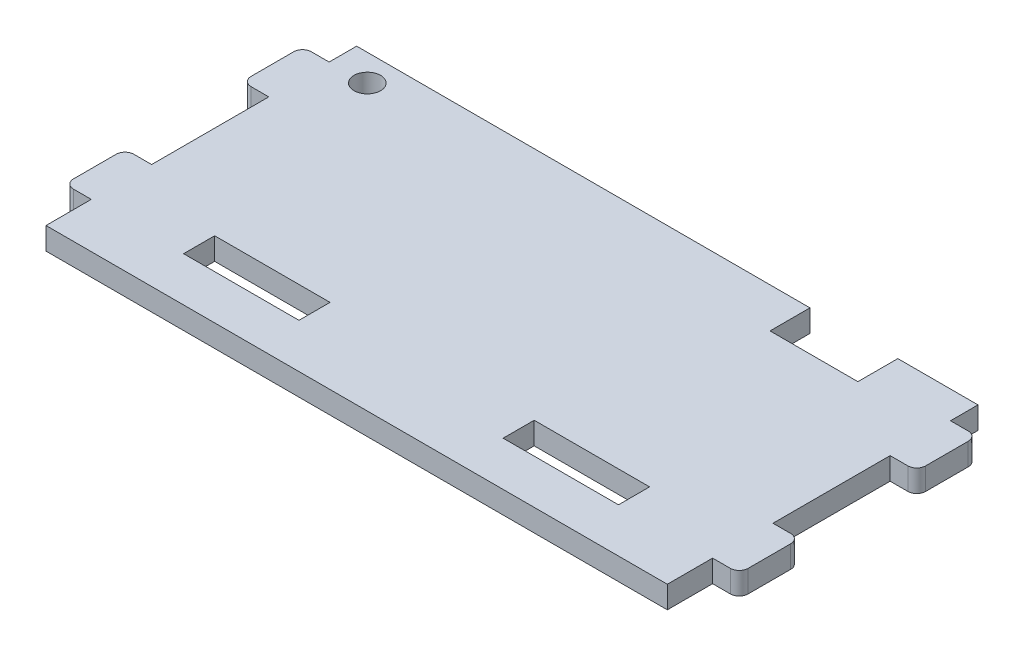
SolidWorks part; units mm, degrees
ref_plane "前视" through (0, 0, 0) normal (0, 0, 1) x (1, 0, 0)
ref_plane "上视" through (0, 0, 0) normal (0, 1, 0) x (1, 0, 0)
ref_plane "右视" through (0, 0, 0) normal (1, 0, 0) x (0, 0, -1)
sketch "草图1" plane through (0, 0, 0) normal (0, 1, 0) x (1, 0, 0)
  line L1 (-38, 17.5) -> (38, 17.5)
  line L2 (-38, 17.5) -> (-38, -17.5)
  line L3 (-38, -17.5) -> (38, -17.5)
  line L4 (38, 17.5) -> (38, -17.5)
  line L5 (-38, 17.5) -> (38, -17.5) construction
  line L6 (-38, -17.5) -> (38, 17.5) construction
  point P0 (0, 0)
  dimension "D1" = 35
  dimension "D2" = 76
extrude "凸台-拉伸1" add sketch "草图1" along normal blind 2.5
sketch "草图2" plane through (0, 2.5, 0) normal (0, 1, 0) x (1, 0, 0)
  line L0 (-38, -17.5) -> (38, -17.5) construction
  line L1 (-24.5, -9) -> (-11.5, -9)
  line L2 (-24.5, -9) -> (-24.5, -12.5)
  line L3 (-24.5, -12.5) -> (-11.5, -12.5)
  line L4 (-11.5, -9) -> (-11.5, -12.5)
  line L5 (-24.5, -9) -> (-11.5, -12.5) construction
  line L6 (-24.5, -12.5) -> (-11.5, -9) construction
  line L7 (-38, 17.5) -> (-38, -17.5) construction
  line L8 (0, 0) -> (0, -2.6782) construction
  line L9 (24.5, -12.5) -> (11.5, -12.5)
  line L10 (11.5, -9) -> (11.5, -12.5)
  line L11 (24.5, -9) -> (11.5, -9)
  line L12 (24.5, -9) -> (24.5, -12.5)
  point P0 (-18, -10.75)
  dimension "D1" = 5
  dimension "D2" = 13.5
  dimension "D3" = 13
  dimension "D4" = 3.5
extrude "切除-拉伸1" cut sketch "草图2" against normal through all
sketch "草图3" plane through (0, 2.5, 0) normal (0, 1, 0) x (1, 0, 0)
  line L0 (-38, -17.5) -> (-35, -17.5)
  line L1 (-38, -17.5) -> (38, -17.5) construction
  line L2 (-35, -17.5) -> (-35, -12.4)
  line L3 (-35, -12.4) -> (-38, -12.4)
  line L4 (-38, 17.5) -> (-38, -17.5) construction
  line L5 (-38, -12.4) -> (-38, -17.5)
  line L6 (-38, 17.5) -> (-35, 17.5)
  line L7 (38, 17.5) -> (-38, 17.5) construction
  line L8 (-35, 17.5) -> (-35, 14.4)
  line L9 (-35, 14.4) -> (-38, 14.4)
  line L10 (-38, 14.4) -> (-38, 17.5)
  line L11 (-38, 7.6) -> (-35, 7.6)
  line L12 (-35, 7.6) -> (-35, -5.6)
  line L13 (-35, -5.6) -> (-38, -5.6)
  line L14 (-38, -5.6) -> (-38, 7.6)
  line L15 (0, 0) -> (0, 5.419) construction
  line L16 (38, -17.5) -> (35, -17.5)
  line L17 (38, -12.4) -> (38, -17.5)
  line L18 (35, -17.5) -> (35, -12.4)
  line L19 (35, -12.4) -> (38, -12.4)
  line L20 (35, -5.6) -> (38, -5.6)
  line L21 (38, -5.6) -> (38, 7.6)
  line L22 (35, 7.6) -> (35, -5.6)
  line L23 (38, 7.6) -> (35, 7.6)
  line L24 (35, 14.4) -> (38, 14.4)
  line L25 (35, 17.5) -> (35, 14.4)
  line L26 (38, 17.5) -> (35, 17.5)
  line L27 (38, 14.4) -> (38, 17.5)
  dimension "D1" = 3
  dimension "D2" = 5.1
  dimension "D3" = 3
  dimension "D4" = 3.1
  dimension "D5" = 3
  dimension "D6" = 6.8
  dimension "D7" = 6.8
extrude "切除-拉伸2" cut sketch "草图3" against normal through all
fillet "圆角1" radius 1 8 edges at (38, 1.25, -14.4) (38, 1.25, -7.6) (38, 1.25, 5.6) (38, 1.25, 12.4) (-38, 1.25, 12.4) (-38, 1.25, 5.6) (-38, 1.25, -7.6) (-38, 1.25, -14.4)
sketch "草图4" plane through (0, 2.5, 0) normal (0, 1, 0) x (1, 0, 0)
  line L0 (35, 17.5) -> (-35, 17.5) construction
  line L1 (35, 17.5) -> (35, 14.4) construction
  line L2 (-35, 14.4) -> (-35, 17.5) construction
  line L3 (18.0812, 14.5) -> (26.9965, 14.5) construction
  line L4 (25.9681, 17.5) -> (25.9681, 13)
  line L5 (25.9681, 13) -> (16.0681, 13)
  line L6 (16.0681, 13) -> (16.0681, 17.5)
  line L7 (16.0681, 17.5) -> (25.9681, 17.5)
  circle A0 centre (-30.8, 14.5) radius 1.5
  point P4 (-35, 15.95)
  point P11 (35, 15.95)
  dimension "D1" = 3
  dimension "D2" = 4.2
  dimension "D3" = 4.5
  dimension "D4" = 9.9
  dimension "D5" = 9.0319
extrude "切除-拉伸3" cut sketch "草图4" against normal through all
